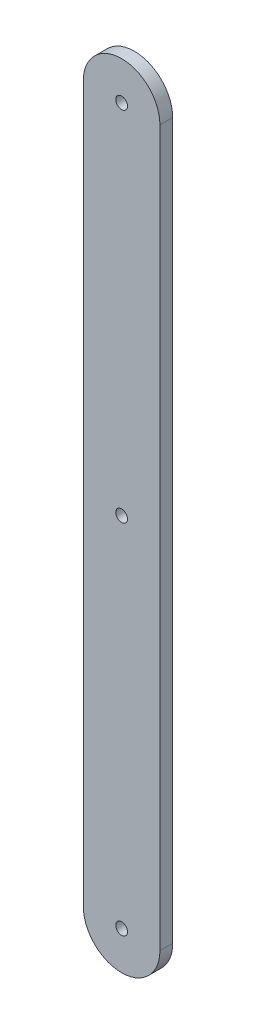
SolidWorks part; units mm, degrees
ref_plane "Front Plane" through (0, 0, 0) normal (0, 0, 1) x (1, 0, 0)
ref_plane "Top Plane" through (0, 0, 0) normal (0, 1, 0) x (1, 0, 0)
ref_plane "Right Plane" through (0, 0, 0) normal (1, 0, 0) x (0, 0, -1)
sketch "Sketch1" plane through (0, 0, 0) normal (0, 0, 1) x (1, 0, 0)
  line L0 (-19.353, 0) -> (-19.353, 177.8)
  line L2 (-0.303, 177.8) -> (-0.303, 0)
  arc A0 (-19.353, 177.8) -> (-0.303, 177.8) centre (-9.828, 177.8) cw
  arc A1 (-19.353, 0) -> (-0.303, 0) centre (-9.828, 0) ccw
  circle A2 centre (-9.828, 0) radius 1.4605
  circle A3 centre (-9.828, 177.8) radius 1.4605
  dimension "D2" = 2.921
  dimension "D3" = 2.921
  dimension "D1" = 177.8
  dimension "D4" = 19.05
extrude "Boss-Extrude1" add sketch "Sketch1" along normal blind 3.175
sketch "Sketch2" plane through (0, 0, 0) normal (0, 0, -1) x (-1, 0, 0)
  line L0 (19.353, 88.9) -> (9.828, 88.9) construction
  line L1 (19.353, 177.8) -> (19.353, 0) construction
  circle A0 centre (9.828, 88.9) radius 1.4605
  dimension "D1" = 9.525
extrude "Cut-Extrude1" cut sketch "Sketch2" against normal blind 3.175
